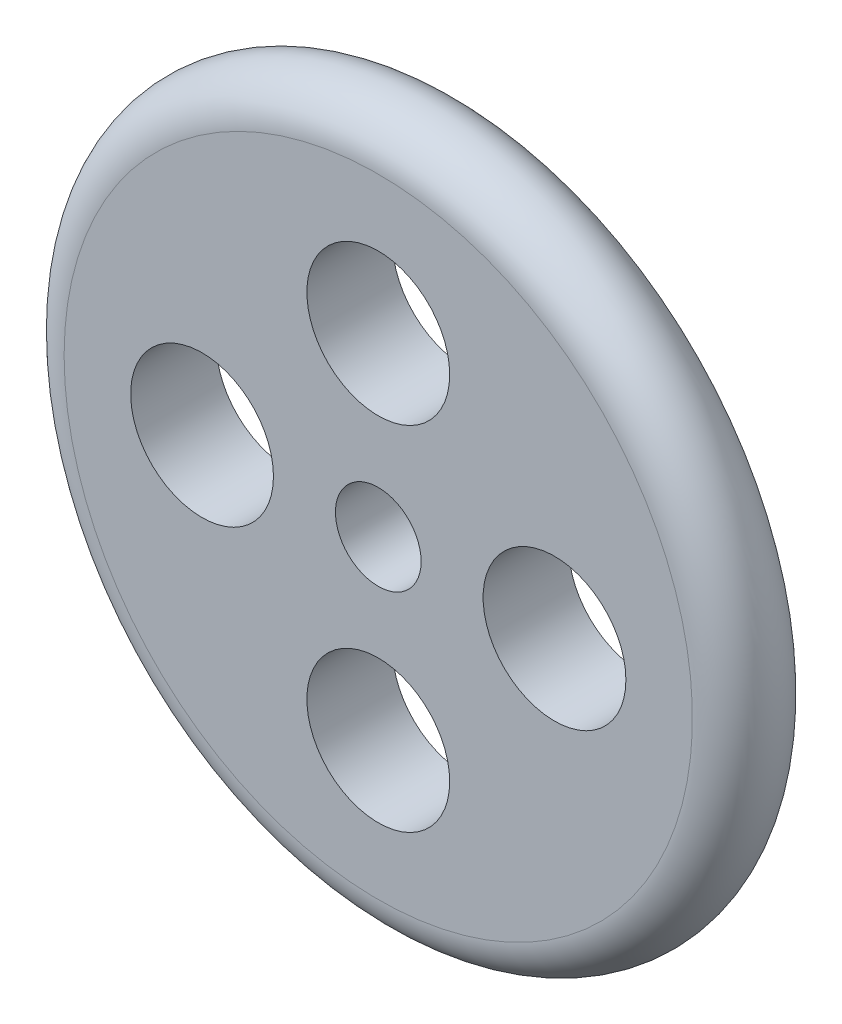
SolidWorks part; units mm, degrees
ref_plane "Front Plane" through (0, 0, 0) normal (0, 0, 1) x (1, 0, 0)
ref_plane "Top Plane" through (0, 0, 0) normal (0, 1, 0) x (1, 0, 0)
ref_plane "Right Plane" through (0, 0, 0) normal (1, 0, 0) x (0, 0, -1)
sketch "Sketch6" plane through (0, 0, 0) normal (0, 1, 0) x (1, 0, 0)
  line L0 (0, 75.7869) -> (110, 75.7869)
  line L1 (0, 75.7869) -> (0, 45.7869)
  line L2 (0, 45.7869) -> (110, 45.7869)
  arc A0 (110, 45.7869) -> (110, 75.7869) centre (110, 60.7869) ccw
revolve "Revolve3" add sketch "Sketch6" angle 360 about L1
sketch "Sketch10" plane through (0, 0, -45.7869) normal (0, 0, 1) x (1, 0, 0)
  circle A0 centre (0, 0) radius 15
  dimension "D1" = 30
extrude "Cut-Extrude1" cut sketch "Sketch10" against normal through all contours A0
sketch "Sketch11" plane through (0, 0, -45.7869) normal (0, 0, 1) x (1, 0, 0)
  line L0 (0, -16.5) -> (0, 16.5) construction
  circle A0 centre (0, 61.7011) radius 25
  circle A1 centre (61.7011, 0) radius 25
  circle A2 centre (0, -61.7011) radius 25
  circle A3 centre (-61.7011, 0) radius 25
  point P13 (0, 0)
  dimension "D2" = 50
  dimension "D1" = 4
extrude "Cut-Extrude2" cut sketch "Sketch11" against normal through all
